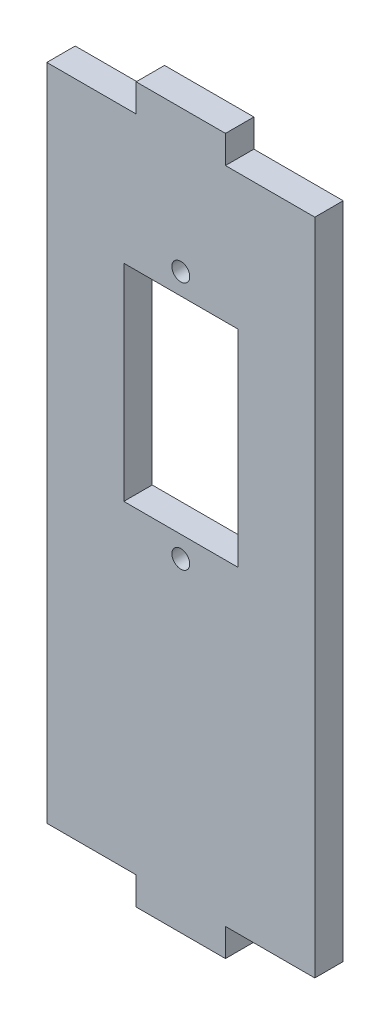
SolidWorks part; units mm, degrees
ref_plane "Front Plane" through (0, 0, 0) normal (0, 0, 1) x (1, 0, 0)
ref_plane "Top Plane" through (0, 0, 0) normal (0, 1, 0) x (1, 0, 0)
ref_plane "Right Plane" through (0, 0, 0) normal (1, 0, 0) x (0, 0, -1)
sketch "Sketch2" plane through (0, 0, 0) normal (0, 0, 1) x (1, 0, 0)
  line L5 (15, -40) -> (-15, -40)
  line L6 (15, -40) -> (15, 40)
  line L11 (15, 40) -> (-15, 40)
  line L12 (-15, -40) -> (-15, 40)
  line L13 (15, -40) -> (-15, 40) construction
  line L14 (15, 40) -> (-15, -40) construction
  point P0 (0, 0)
  dimension "D1" = 30
  dimension "D2" = 80
extrude "Boss-Extrude1" add sketch "Sketch2" along normal blind 3.18
sketch "Sketch4" plane through (0, 0, 3.18) normal (0, 0, 1) x (1, 0, 0)
  line L0 (15, 40) -> (-15, 40) construction
  line L1 (5, 40) -> (15, 40)
  line L2 (5, 40) -> (5, 36.88)
  line L3 (5, 36.88) -> (15, 36.88)
  line L4 (15, 40) -> (15, 36.88)
  line L5 (15, -40) -> (15, 40) construction
  dimension "D1" = 3.12
  dimension "D2" = 10
extrude "Cut-Extrude1" cut sketch "Sketch4" against normal up to surface (3.18 mm away) up to face at (0, 0, 0)
mirror "Mirror1" about plane through (0, 0, 0) normal (1, 0, 0) of "Cut-Extrude1"
mirror "Mirror2" about plane through (0, 0, 0) normal (0, 1, 0) of "Mirror1", "Cut-Extrude1"
sketch "Sketch5" plane through (0, 0, 0) normal (0, 0, -1) x (-1, 0, 0)
  line L0 (-15, -36.88) -> (-15, 36.88) construction
  line L1 (6.08, 21.4254) -> (-6.08, 21.4254) construction
  line L2 (6.08, 21.4254) -> (6.08, -1.066) construction
  line L3 (6.08, -1.066) -> (-6.08, -1.066) construction
  line L4 (-6.08, 21.4254) -> (-6.08, -1.066) construction
  line L7 (-5, 40) -> (5, 40) construction
  line L8 (5, -40) -> (-5, -40) construction
  line L12 (15, 36.88) -> (15, -36.88) construction
  line L13 (6.38, 21.7254) -> (-6.38, 21.7254)
  line L14 (-6.38, 21.7254) -> (-6.38, -1.366)
  line L15 (6.38, -1.366) -> (-6.38, -1.366)
  line L16 (6.38, 21.7254) -> (6.38, -1.366)
  dimension "D1" = 8.92
  dimension "D2" = 8.92
  dimension "D3" = 18.5746
  dimension "D4" = 38.934
  dimension "D6" = 12.76
  dimension "D5" = 0.3
extrude "Cut-Extrude2" cut sketch "Sketch5" against normal up to surface (3.18 mm away) up to face at (0, 0, 3.18)
sketch "Sketch6" plane through (0, 0, 0) normal (0, 0, -1) x (-1, 0, 0)
  line L0 (-15, -36.88) -> (-15, 36.88) construction
  line L2 (15, 36.88) -> (15, -36.88) construction
  line L3 (-6.38, -1.366) -> (6.38, -1.366) construction
  line L4 (6.38, 21.7254) -> (-6.38, 21.7254) construction
  circle A0 centre (0, 24.1004) radius 1
  circle A1 centre (0, -3.746) radius 1
  dimension "D1" = 2
  dimension "D2" = 2
  dimension "D3" = 15
  dimension "D4" = 15
  dimension "D5" = 15
  dimension "D6" = 15
  dimension "D7" = 2.38
  dimension "D8" = 2.375
extrude "Cut-Extrude3" cut sketch "Sketch6" against normal through all
